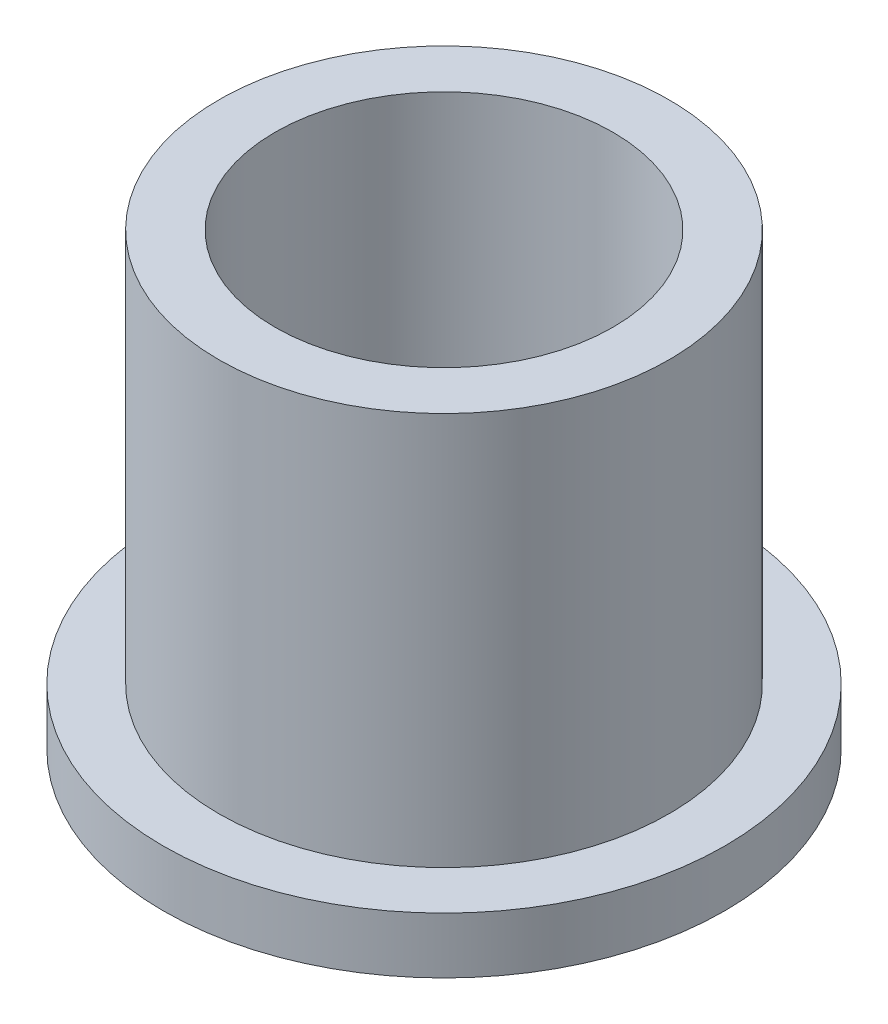
SolidWorks part; units mm, degrees
ref_plane "Front" through (0, 0, 0) normal (0, 0, 1) x (1, 0, 0)
ref_plane "Top" through (0, 0, 0) normal (0, 1, 0) x (1, 0, 0)
ref_plane "Right" through (0, 0, 0) normal (1, 0, 0) x (0, 0, -1)
sketch "Sketch1" plane through (0, 0, 0) normal (0, 1, 0) x (1, 0, 0)
  circle A0 centre (0, 0) radius 4.7752
  circle A1 centre (0, 0) radius 6.3627
  circle A2 centre (0, 0) radius 7.9375
  dimension "ID" = 9.5504
  dimension "OD" = 12.7254
  dimension "FlangeOD" = 15.875
sketch "Sketch2" plane through (0, 0, 0) normal (0, 1, 0) x (1, 0, 0)
  circle A0 centre (0, 0) radius 4.7752 construction
  circle A1 centre (0, 0) radius 6.3627 construction
  circle A2 centre (0, 0) radius 4.7752
  circle A3 centre (0, 0) radius 6.3627
extrude "Boss-Extrude1" add sketch "Sketch2" along normal blind 12.7
sketch "Sketch3" plane through (0, 0, 0) normal (0, 1, 0) x (1, 0, 0)
  circle A0 centre (0, 0) radius 7.9375 construction
  circle A1 centre (0, 0) radius 6.3627 construction
  circle A2 centre (0, 0) radius 7.9375
  circle A3 centre (0, 0) radius 6.3627
extrude "Boss-Extrude2" add sketch "Sketch3" along normal blind 1.5875
